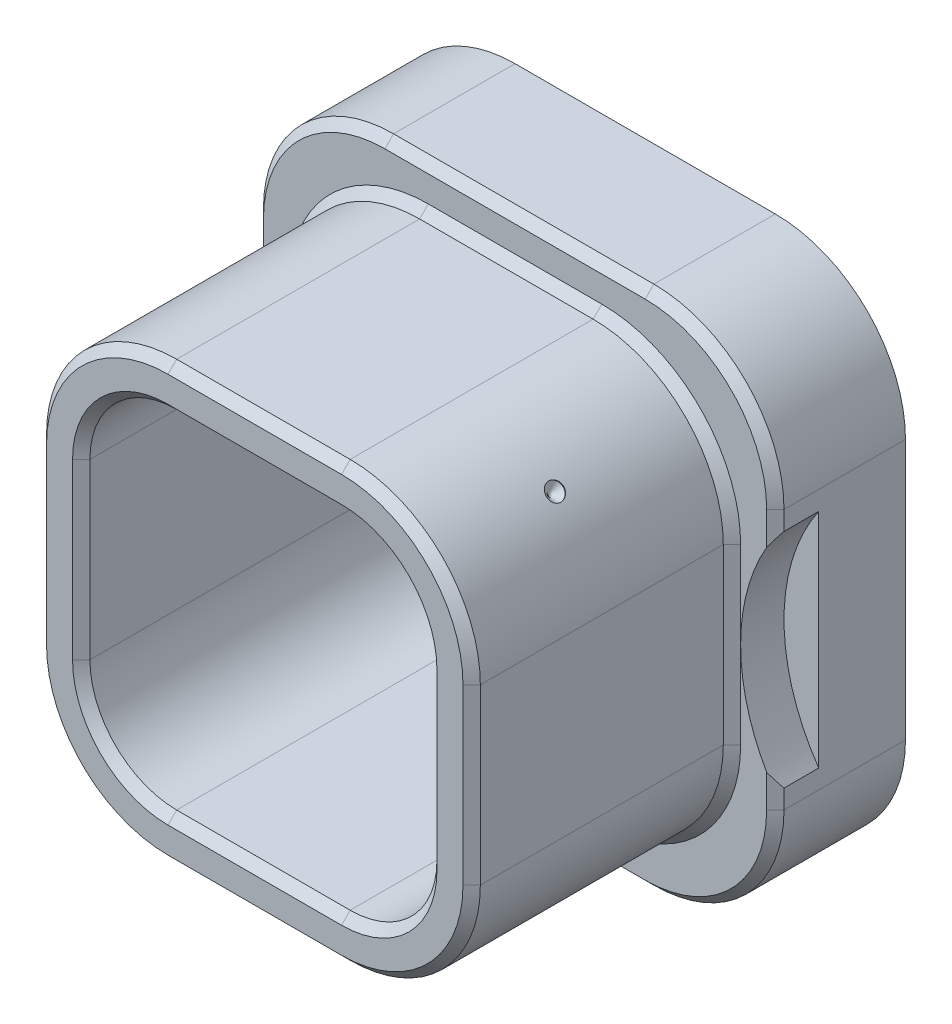
SolidWorks part; units mm, degrees
ref_plane "Ebene vorne" through (0, 0, 0) normal (0, 0, 1) x (1, 0, 0)
ref_plane "Ebene oben" through (0, 0, 0) normal (0, 1, 0) x (1, 0, 0)
ref_plane "Ebene rechts" through (0, 0, 0) normal (1, 0, 0) x (0, 0, -1)
sketch "Skizze1" plane through (0, 0, 0) normal (0, 0, 1) x (1, 0, 0)
  line L5 (-3, -3) -> (3, -3)
  line L6 (-3, -3) -> (-3, 3)
  line L7 (-3, 3) -> (3, 3)
  line L8 (3, -3) -> (3, 3)
  line L9 (-3, -3) -> (3, 3) construction
  line L10 (-3, 3) -> (3, -3) construction
  point P0 (0, 0)
  dimension "D1" = 6
  dimension "D2" = 6
extrude "Aufsatz-Linear austragen1" add sketch "Skizze1" against normal blind 1.5
sketch "Skizze2" plane through (0, 0, 0) normal (0, 0, -1) x (-1, 0, 0)
  line L0 (-2.5, 2.5) -> (2.5, 2.5)
  line L1 (-2.5, 2.5) -> (-2.5, -2.5)
  line L2 (-2.5, -2.5) -> (2.5, -2.5)
  line L3 (2.5, 2.5) -> (2.5, -2.5)
  line L4 (-2.5, 2.5) -> (2.5, -2.5) construction
  line L5 (-2.5, -2.5) -> (2.5, 2.5) construction
  line L6 (-1.9742, 1.9493) -> (2.0255, -2) construction
  line L7 (-1.9997, -1.9745) -> (2.0255, 2) construction
  point P0 (0, 0)
  point P5 (0, 0)
  dimension "D1" = 5
  dimension "D2" = 5
  dimension "D3" = 4
  dimension "D4" = 4
extrude "Aufsatz-Linear austragen2" add sketch "Skizze2" against normal blind 3
sketch "Skizze3" plane through (0, 0, 3) normal (0, 0, 1) x (1, 0, 0)
  line L0 (-2, 2) -> (2, 2)
  line L1 (-2, 2) -> (-2, -2)
  line L2 (-2, -2) -> (2, -2)
  line L3 (2, 2) -> (2, -2)
  line L4 (-2, 2) -> (2, -2) construction
  line L5 (-2, -2) -> (2, 2) construction
  point P0 (0, 0)
  dimension "D1" = 4
  dimension "D2" = 4
extrude "Schnitt-Linear austragen1" cut sketch "Skizze3" against normal blind 3.5
fillet "Verrundung1" radius 1 4 edges at (-2, -2, 1.25) (2, -2, 1.25) (2, 2, 1.25) (-2, 2, 1.25)
fillet "Verrundung2" radius 1.5 4 edges at (-2.5, -2.5, 1.5) (2.5, -2.5, 1.5) (2.5, 2.5, 1.5) (-2.5, 2.5, 1.5)
fillet "Verrundung3" radius 1.5 4 edges at (-3, -3, -0.75) (3, -3, -0.75) (3, 3, -0.75) (-3, 3, -0.75)
chamfer "Fase1" distance 0.1 angle 45 32 edges at (2.5607, -2.5607, 0) (3, 0, 0) (2.5607, 2.5607, 0) (0, 3, 0) (-2.5607, 2.5607, 0) (-3, 0, 0) (-2.5607, -2.5607, 0) (0, -3, 0) (2.0607, -2.0607, 3) (2.5, 0, 3) (2.0607, 2.0607, 3) (0, 2.5, 3) (-2.0607, 2.0607, 3) (-2.5, 0, 3) (-2.0607, -2.0607, 3) (0, -2.5, 3) (1.7071, 1.7071, 3) (0, 2, 3) (-1.7071, 1.7071, 3) (-2, 0, 3) (-1.7071, -1.7071, 3) (0, -2, 3) (1.7071, -1.7071, 3) (2, 0, 3) (2.0607, 2.0607, 0) (0, 2.5, 0) (-2.0607, 2.0607, 0) (-2.5, 0, 0) (-2.0607, -2.0607, 0) (0, -2.5, 0) (2.0607, -2.0607, 0) (2.5, 0, 0)
sketch "Skizze4" plane through (0, 0, 0) normal (0, 0, 1) x (1, 0, 0)
  line L0 (0, 0) -> (0, 1.8559) construction
  line L1 (0, 0) -> (2.5607, 2.5607) construction
  dimension "D1" = 45
ref_plane "Ebene1" through (2.0607, 2.0607, 0) normal (0.7071, 0.7071, 0) x (0.7071, -0.7071, 0)
hole_wizard "Ø0.2 (0.2) Durchmesser Bohrung5" positions "Skizze5" profile "Skizze6" hole size "Ø0.2" standard "DIN"
sketch "Skizze5" plane through (2.0607, 2.0607, 0) normal (0.7071, 0.7071, 0) x (0.7071, -0.7071, 0)
  line L0 (1.0607, -0.1) -> (-1.0607, -0.1) construction
  point P0 (0, -1.6)
  dimension "D1" = 1.5
sketch "Skizze6" plane through (2.0607, 2.0607, 1.6) normal (0, 0, 1) x (-0.7071, 0.7071, 0)
  line L0 (0, 0) -> (0, 0.11)
  line L1 (0, 0.11) -> (0.1, 0.01)
  line L2 (0.1, 0.01) -> (0.1, 0)
  line L5 (0.1, 0) -> (0, 0)
  line L10 (0, 0.11) -> (-0.1, 0.01) construction
  line L11 (0, -6.35) -> (0, 107.95) construction
  dimension "Bohrerdurchmesser" = 0.2
  dimension "Bohrungstiefe" = 0.01
  dimension "Spitzenwinkel" = 90
sketch "Skizze7" plane through (0, 0, 0) normal (0, 0, 1) x (1, 0, 0)
  line L0 (-2.6, -1) -> (-2.6, 1) construction
  line L3 (0, -2.475) -> (0, 2.475) construction
  circle A0 centre (-4.85, 0) radius 2.25
  circle A2 centre (4.85, 0) radius 2.25
  dimension "D1" = 4.5
extrude "Schnitt-Linear austragen2" cut sketch "Skizze7" against normal blind 0.5
